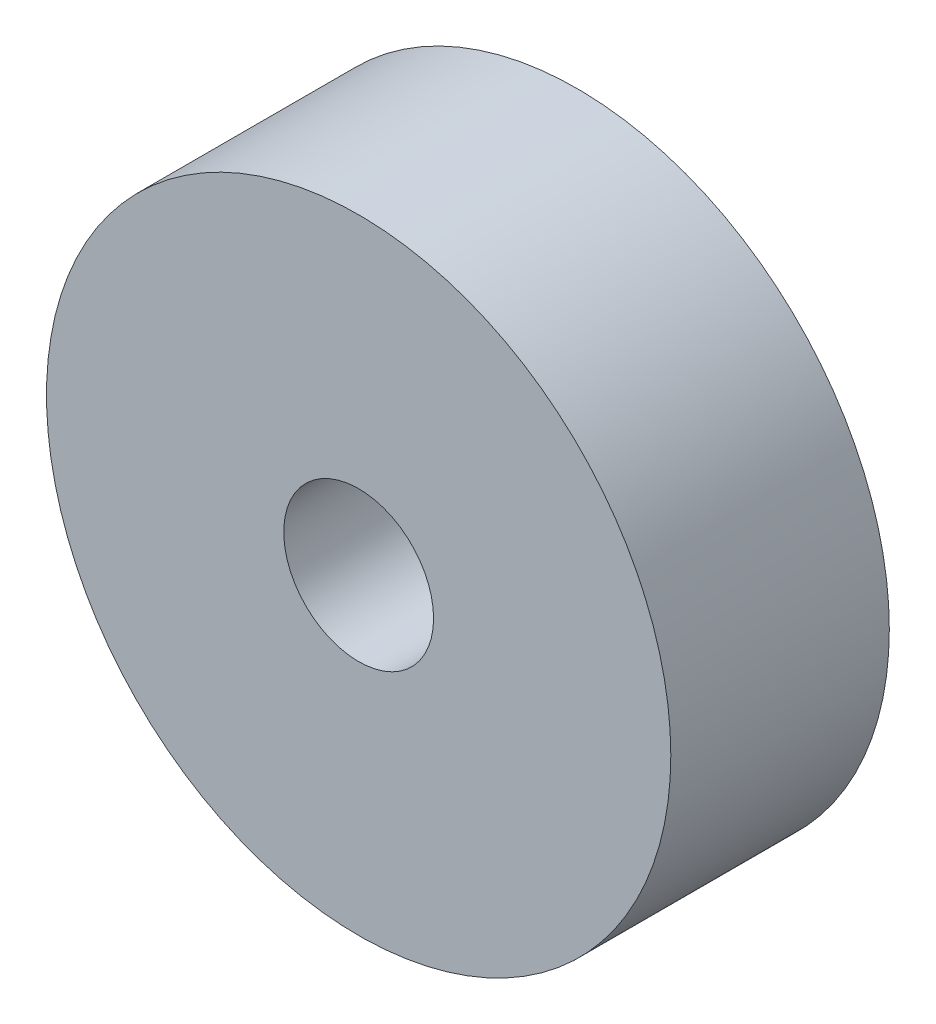
SolidWorks part; units mm, degrees
ref_plane "Alzado" through (0, 0, 0) normal (0, 0, 1) x (1, 0, 0)
ref_plane "Planta" through (0, 0, 0) normal (0, 1, 0) x (1, 0, 0)
ref_plane "Vista lateral" through (0, 0, 0) normal (1, 0, 0) x (0, 0, -1)
ref_plane "Plane1" through (0, -7.8054, 0) normal (0, 1, 0) x (1, 0, 0)
sketch "Sketch1" plane through (0, -7.8054, 0) normal (0, 1, 0) x (1, 0, 0)
  line L0 (7.5844, 1.8) -> (7.5844, 2.15)
  line L1 (7.5844, 2.15) -> (7.3844, 2.15)
  line L2 (7.2186, 2.1) -> (7.2044, 2.1)
  line L3 (7.2044, 2.1) -> (7.2044, 1.8)
  line L4 (7.2044, 1.8) -> (7.5844, 1.8)
  line L5 (7.0844, 2.15) -> (7.0844, 1.8) construction
  arc A0 (7.3844, 2.15) -> (7.2186, 2.1) centre (7.2186, 2.4) cw
  dimension "D1" = 0.3
  dimension "D2" = 0.12
  dimension "D3" = 0.1342
  dimension "D4" = 0.3
  dimension "D5" = 0.5
  dimension "D6" = 0.3
revolve "Revolve1" add sketch "Sketch1" angle 360 about L5
